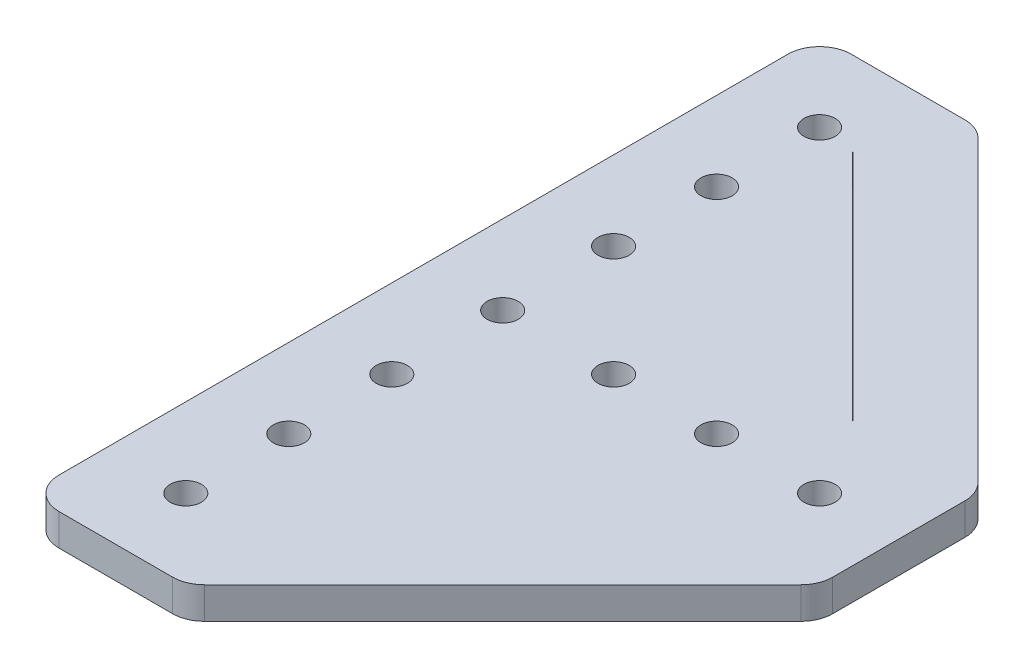
SolidWorks part; units mm, degrees
material "ABS"
ref_plane "Front Plane" through (0, 0, 0) normal (0, 0, 1) x (1, 0, 0)
ref_plane "Top Plane" through (0, 0, 0) normal (0, 1, 0) x (1, 0, 0)
ref_plane "Right Plane" through (0, 0, 0) normal (1, 0, 0) x (0, 0, -1)
sketch "Sketch1" plane through (0, 0, 0) normal (0, 1, 0) x (1, 0, 0)
  line L0 (0, 0) -> (0, 76.2)
  line L1 (0, 76.2) -> (25.4, 76.2)
  line L2 (25.4, 76.2) -> (76.2, 25.4)
  line L3 (76.2, 25.4) -> (76.2, 0)
  line L4 (76.2, 0) -> (0, 0)
  line L5 (25.4, 76.2) -> (25.4, 25.4) construction
  line L6 (25.4, 25.4) -> (76.2, 25.4) construction
  line L7 (76.2, 12.7) -> (12.7, 12.7) construction
  line L8 (12.7, 12.7) -> (12.7, 76.2) construction
  circle A0 centre (12.7, 63.5) radius 2.5
  circle A1 centre (63.5, 12.7) radius 2.5
  circle A2 centre (12.7, 46.99) radius 2.5
  circle A3 centre (12.7, 30.48) radius 2.5
  circle A4 centre (46.99, 12.7) radius 2.5
  circle A5 centre (30.48, 12.7) radius 2.5
  circle A6 centre (12.7, 12.7) radius 2.5
  dimension "D3" = 5
  dimension "D1" = 25.4
  dimension "D2" = 76.2
  dimension "D4" = 12.7
  dimension "D5" = 12.7
  dimension "D6" = 3
  dimension "D7" = 3
extrude "Boss-Extrude1" add sketch "Sketch1" along normal blind 5.08
fillet "Fillet1" radius 5.08 1 edges at (0, 2.54, 0)
fillet "Fillet2" radius 5.08 4 edges at (25.4, 2.54, -76.2) (0, 2.54, -76.2) (76.2, 2.54, 0) (76.2, 2.54, -25.4)
sketch "Sketch2" plane through (0, 5.08, 0) normal (0, 1, 0) x (1, 0, 0)
  line L0 (18.7727, 62.7399) -> (62.7399, 18.7727)
  line L1 (50.8, 50.8) -> (-5.35, -5.35) construction
  line L2 (74.7121, 26.8879) -> (26.8879, 74.7121) construction
  line L3 (18.7656, 62.7328) -> (62.7328, 18.7656)
  line L4 (18.7798, 62.747) -> (62.747, 18.7798)
  line L5 (18.7656, 41.7984) -> (41.7984, 18.7656) construction
  line L6 (18.7638, 41.7966) -> (41.7966, 18.7638)
  line L7 (18.7674, 41.8002) -> (41.8002, 18.7674)
  line L8 (24.4426, 18.5467) -> (18.5467, 24.4426) construction
  line L9 (24.4444, 18.5485) -> (18.5485, 24.4444)
  line L10 (24.4408, 18.5449) -> (18.5449, 24.4408)
  arc A0 (18.7656, 62.7328) -> (18.7798, 62.747) centre (18.7727, 62.7399) cw
  arc A1 (62.7328, 18.7656) -> (62.747, 18.7798) centre (62.7399, 18.7727) ccw
  arc A2 (18.7638, 41.7966) -> (18.7674, 41.8002) centre (18.7656, 41.7984) cw
  arc A3 (41.7966, 18.7638) -> (41.8002, 18.7674) centre (41.7984, 18.7656) ccw
  arc A4 (24.4444, 18.5485) -> (24.4408, 18.5449) centre (24.4426, 18.5467) cw
  arc A5 (18.5485, 24.4444) -> (18.5449, 24.4408) centre (18.5467, 24.4426) ccw
  point P6 (40.7563, 40.7563)
  point P16 (30.282, 30.282)
  point P23 (21.4946, 21.4946)
  dimension "D1" = 0.01
  dimension "D2" = 0.01
  dimension "D3" = 0.0025
  dimension "D4" = 0.0025
  dimension "D5" = 0.0025
  dimension "D6" = 0.0025
extrude "Cut-Extrude1" cut sketch "Sketch2" against normal through all
ref_plane "Plane1" through (0, 0, -12.7) normal (0, 0, 1) x (1, 0, 0)
mirror "Mirror1" about plane through (0, 0, -12.7) normal (0, 0, 1) of bodies 102
